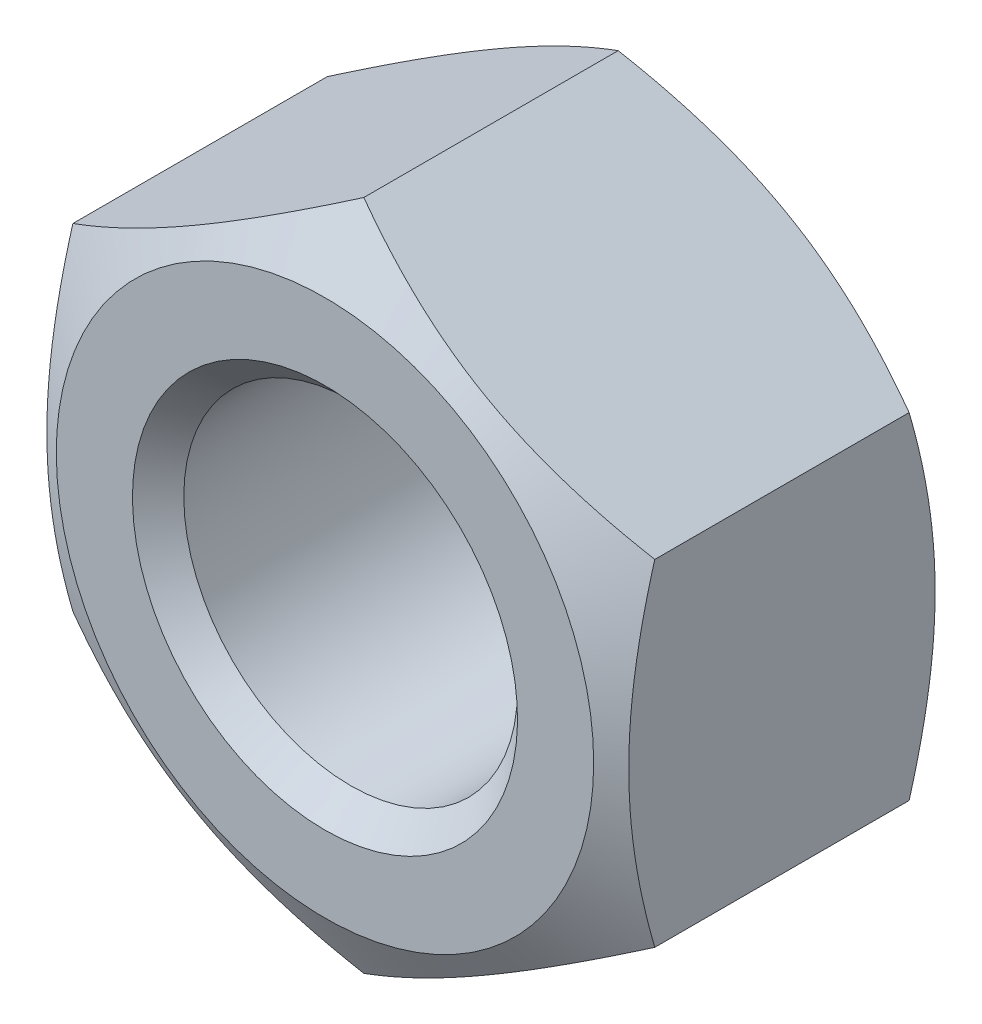
SolidWorks part; units mm, degrees
ref_plane "Front Plane" through (0, 0, 0) normal (0, 0, 1) x (1, 0, 0)
ref_plane "Top Plane" through (0, 0, 0) normal (0, 1, 0) x (1, 0, 0)
ref_plane "Right Plane" through (0, 0, 0) normal (1, 0, 0) x (0, 0, -1)
sketch "Sketch1" plane through (0, 0, 0) normal (0, 0, 1) x (1, 0, 0)
  line L0 (0, 0) -> (0, 19.6299) construction
  line L1 (0, 19.6299) -> (-17, 9.815)
  line L2 (-17, 9.815) -> (-17, -9.815)
  line L3 (-17, -9.815) -> (0, -19.6299)
  line L4 (0, -19.6299) -> (17, -9.815)
  line L5 (17, -9.815) -> (17, 9.815)
  line L6 (17, 9.815) -> (0, 19.6299)
  circle A0 centre (0, 0) radius 17 construction
  dimension "S DIM" = 34
extrude "Boss-Extrude1" add sketch "Sketch1" against normal blind 19.4
sketch "Sketch4" plane through (0, 0, 0) normal (1, 0, 0) x (0, 0, -1)
  line L0 (19.4, 19.6299) -> (17.1311, 19.6299)
  line L1 (19.4, 19.6299) -> (0, 19.6299) construction
  line L2 (17.1311, 19.6299) -> (19.4, 15.7)
  line L4 (19.4, 15.7) -> (19.4, 19.6299)
  line L5 (0, 0) -> (3.2979, 0) construction
  line L6 (0, 19.6299) -> (2.2689, 19.6299)
  line L7 (2.2689, 19.6299) -> (0, 15.7)
  line L9 (0, 15.7) -> (0, 19.6299)
  dimension "SAME S 1" = 31.4
  dimension "D2" = 30
  dimension "SAME S 2" = 31.4
  dimension "D4" = 30
revolve "Cut-Revolve1" cut sketch "Sketch4" angle 360 about L5
sketch "Sketch5" plane through (0, 0, 0) normal (1, 0, 0) x (0, 0, -1)
  line L0 (0, 0) -> (19.4, 0) construction
  line L1 (0, 0) -> (0, 11.25)
  line L2 (0, 15.7) -> (0, -15.7) construction
  line L3 (0, 11.25) -> (1.5, 9.75)
  line L4 (1.5, 9.75) -> (17.9, 9.75)
  line L5 (17.9, 9.75) -> (19.4, 11.25)
  line L6 (19.4, 11.25) -> (19.4, 0)
  line L8 (19.4, -15.7) -> (19.4, 15.7) construction
  line L9 (19.4, 0) -> (0, 0)
  dimension "D1" = 45
  dimension "Hole2" = 22.5
  dimension "Hole1" = 19.5
revolve "Cut-Revolve2" cut sketch "Sketch5" angle 360 about L0
cosmetic thread "Cosmetic Thread1" parameters "D2"=22
